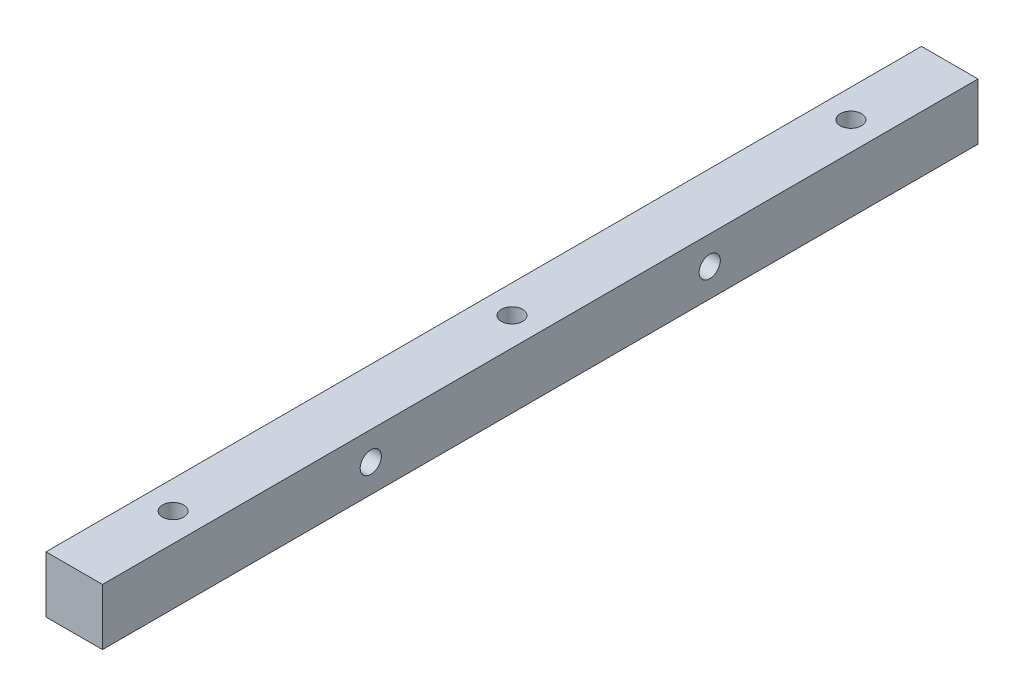
SolidWorks part; units mm, degrees
ref_plane "Alzado" through (0, 0, 0) normal (0, 0, 1) x (1, 0, 0)
ref_plane "Planta" through (0, 0, 0) normal (0, 1, 0) x (1, 0, 0)
ref_plane "Vista lateral" through (0, 0, 0) normal (1, 0, 0) x (0, 0, -1)
sketch "Croquis1" plane through (0, 0, 0) normal (0, 0, 1) x (1, 0, 0)
  line L1 (-5, 5) -> (5, 5)
  line L2 (-5, 5) -> (-5, -5)
  line L3 (-5, -5) -> (5, -5)
  line L4 (5, 5) -> (5, -5)
  line L5 (-5, 5) -> (5, -5) construction
  line L6 (-5, -5) -> (5, 5) construction
  point P0 (0, 0)
  dimension "D1" = 10
  dimension "D2" = 10
extrude "Saliente-Extruir1" add sketch "Croquis1" along normal mid plane 155
sketch "Croquis2" plane through (0, 5, 0) normal (0, 1, 0) x (1, 0, 0)
  line L0 (0, -60) -> (0, 60) construction
  point P0 (0, 0)
  point P4 (0, 0)
  point P5 (0, 60)
  point P7 (0, -60)
  dimension "D1" = 120
sketch "Croquis3" plane through (-5, 0, 0) normal (-1, 0, 0) x (0, 0, 1)
  line L0 (-30, 0) -> (30, 0) construction
  point P4 (0, 0)
  dimension "D1" = 60
hole_wizard "Taladro de margen para M31" positions "Croquis4" profile "Croquis5" hole size "M3" standard "DIN" end condition through all
sketch "Croquis4" plane through (0, 5, 0) normal (0, 1, 0) x (1, 0, 0)
  point P0 (0, -60)
  point P3 (0, 0)
  point P6 (0, 60)
sketch "Croquis5" plane through (0, 5, 60) normal (1, 0, 0) x (0, 0, 1)
  line L0 (0, 0) -> (0, 10)
  line L1 (0, 10) -> (1.875, 10)
  line L2 (1.875, 10) -> (1.875, 0)
  line L5 (1.875, 0) -> (0, 0)
  line L11 (0, -6.35) -> (0, 107.95) construction
  dimension "Diámetro de taladro hasta el siguiente" = 3.75
  dimension "Profundidad de taladro hasta el siguiente" = 10
sketch "Croquis7" plane through (0, -5, 0) normal (0, -1, 0) x (1, 0, 0)
  line L1 (2.7713, -58.4) -> (0, -56.8)
  line L2 (0, -56.8) -> (-2.7713, -58.4)
  line L3 (-2.7713, -58.4) -> (-2.7713, -61.6)
  line L4 (-2.7713, -61.6) -> (0, -63.2)
  line L5 (0, -63.2) -> (2.7713, -61.6)
  line L6 (2.7713, -61.6) -> (2.7713, -58.4)
  line L7 (2.7713, -1.6) -> (2.7713, 1.6)
  line L8 (2.7713, 1.6) -> (0, 3.2)
  line L9 (0, 3.2) -> (-2.7713, 1.6)
  line L10 (-2.7713, 1.6) -> (-2.7713, -1.6)
  line L11 (-2.7713, -1.6) -> (0, -3.2)
  line L12 (0, -3.2) -> (2.7713, -1.6)
  line L13 (2.7713, 58.4) -> (2.7713, 61.6)
  line L14 (2.7713, 61.6) -> (0, 63.2)
  line L15 (0, 63.2) -> (-2.7713, 61.6)
  line L16 (-2.7713, 61.6) -> (-2.7713, 58.4)
  line L17 (-2.7713, 58.4) -> (0, 56.8)
  line L18 (0, 56.8) -> (2.7713, 58.4)
  circle A0 centre (0, -60) radius 2.7713 construction
  circle A1 centre (0, 0) radius 2.7713 construction
  circle A2 centre (0, 60) radius 2.7713 construction
  dimension "D1" = 3.2
extrude "Cortar-Extruir1" cut sketch "Croquis7" against normal blind 3
hole_wizard "Taladro de margen para M32" positions "Croquis8" profile "Croquis9" hole size "M3" standard "DIN" end condition through all
sketch "Croquis8" plane through (-5, 0, 0) normal (-1, 0, 0) x (0, 0, 1)
  point P0 (-30, 0)
  point P3 (30, 0)
sketch "Croquis9" plane through (-5, 0, -30) normal (0, 1, 0) x (0, 0, 1)
  line L0 (0, 0) -> (0, 10)
  line L1 (0, 10) -> (1.875, 10)
  line L2 (1.875, 10) -> (1.875, 0)
  line L5 (1.875, 0) -> (0, 0)
  line L11 (0, -6.35) -> (0, 107.95) construction
  dimension "Diámetro de taladro hasta el siguiente" = 3.75
  dimension "Profundidad de taladro hasta el siguiente" = 10
sketch "Croquis10" plane through (-5, 0, 0) normal (-1, 0, 0) x (0, 0, 1)
  line L1 (-28.4, -2.7713) -> (-26.8, 0)
  line L2 (-26.8, 0) -> (-28.4, 2.7713)
  line L3 (-28.4, 2.7713) -> (-31.6, 2.7713)
  line L4 (-31.6, 2.7713) -> (-33.2, 0)
  line L5 (-33.2, 0) -> (-31.6, -2.7713)
  line L6 (-31.6, -2.7713) -> (-28.4, -2.7713)
  line L7 (31.6, -2.7713) -> (33.2, 0)
  line L8 (33.2, 0) -> (31.6, 2.7713)
  line L9 (31.6, 2.7713) -> (28.4, 2.7713)
  line L10 (28.4, 2.7713) -> (26.8, 0)
  line L11 (26.8, 0) -> (28.4, -2.7713)
  line L12 (28.4, -2.7713) -> (31.6, -2.7713)
  circle A0 centre (-30, 0) radius 2.7713 construction
  circle A1 centre (30, 0) radius 2.7713 construction
  dimension "D1" = 3.2
extrude "Cortar-Extruir2" cut sketch "Croquis10" against normal blind 3
sketch "Croquis11" plane through (-5, 0, 0) normal (-1, 0, 0) x (0, 0, 1)
  line L0 (-15, 0) -> (15, 0) construction
  point P0 (0, 0)
  point P4 (0, 0)
  dimension "D1" = 30
hole_wizard "Taladro de margen para M33" positions "Croquis12" profile "Croquis13" hole size "M3" standard "DIN"
sketch "Croquis12" plane through (-5, 0, 0) normal (-1, 0, 0) x (0, 0, 1)
  point P0 (-15, 0)
  point P7 (0, 0)
sketch "Croquis13" plane through (-5, 0, -15) normal (0, 1, 0) x (0, 0, 1)
  line L0 (0, 0) -> (0, 7.1266)
  line L1 (0, 7.1266) -> (1.875, 6)
  line L2 (1.875, 6) -> (1.875, 0)
  line L5 (1.875, 0) -> (0, 0)
  line L10 (0, 7.1266) -> (-1.875, 6) construction
  line L11 (0, -6.35) -> (0, 107.95) construction
  dimension "Diámetro de taladro" = 3.75
  dimension "Profundidad de taladro" = 6
  dimension "Ángulo de perforador" = 118
ref_plane "Plano1" through (0, 0, 0) normal (-1, 0, 0) x (0, 0, 1)
sketch "Croquis15" plane through (0, 0, 0) normal (-1, 0, 0) x (0, 0, 1)
  line L0 (-18.6, 0) -> (-18.6, -5)
  line L1 (-11.4, 0) -> (-13.2, 3.1177)
  line L2 (-13.2, 3.1177) -> (-16.8, 3.1177)
  line L3 (-16.8, 3.1177) -> (-18.6, 0)
  line L4 (-18.6, 0) -> (-16.8, -3.1177)
  line L5 (-16.8, -3.1177) -> (-13.2, -3.1177)
  line L6 (-13.2, -3.1177) -> (-11.4, 0)
  line L7 (77.5, -5) -> (-77.5, -5) construction
  line L8 (-18.6, -5) -> (-11.4, -5)
  line L9 (-11.4, -5) -> (-11.4, 0)
  line L10 (0, 0) -> (0, -5) construction
  circle A0 centre (-15, 0) radius 3.1177 construction
  dimension "D1" = 3.6
extrude "Cortar-Extruir3" cut sketch "Croquis15" against normal blind 3.2 contours L8 L9 L6 L5 L4 L0 | L5 L6 L1 L2 L3 L4
pattern_linear "MatrizL1" count 3 spacing 30 along (0, 0, 1) count 2 spacing 30 along (0, 0, -1) of "Cortar-Extruir3", "Taladro de margen para M33"
